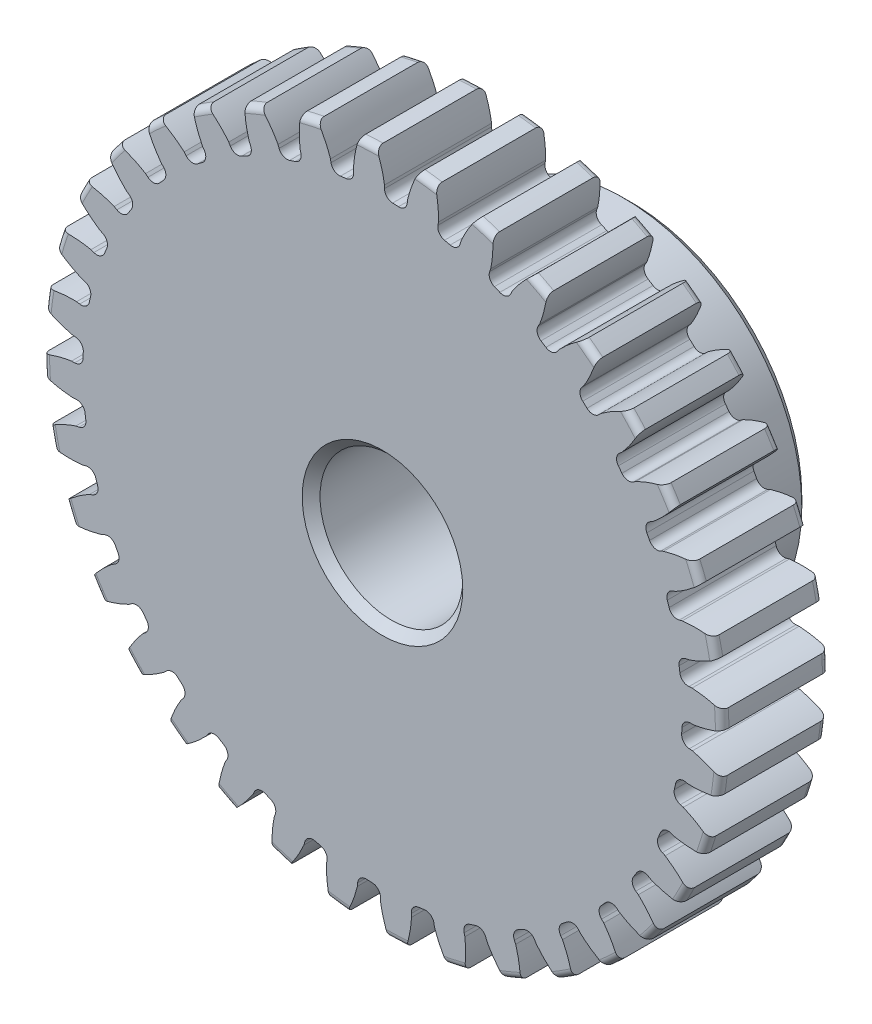
SolidWorks part; units mm, degrees
ref_plane "Front" through (0, 0, 0) normal (0, 0, 1) x (1, 0, 0)
ref_plane "Top" through (0, 0, 0) normal (0, 1, 0) x (1, 0, 0)
ref_plane "Right" through (0, 0, 0) normal (1, 0, 0) x (0, 0, -1)
sketch "Sketch1" plane through (0, 0, 0) normal (0, 0, 1) x (1, 0, 0)
  line L0 (-457.2, 0) -> (457.2, 0) construction
  circle A0 centre (0, 0) radius 15.113
  circle A1 centre (0, 0) radius 14.2875 construction
  circle A3 centre (0, 0) radius 13.3271 construction
  dimension "D1" = 1.7859
  dimension "OD" = 30.226
  dimension "Ptich Dia" = 28.575
  dimension "Root Dia" = 26.6541
  dimension "D3" = 0.8255
  dimension "Number of Teeth" = 914.4
extrude "Boss-Extrude1" add sketch "Sketch1" against normal blind 4.7625
sketch "Sketch2" plane through (0, 0, 0) normal (1, 0, 0) x (0, 0, -1)
  line L0 (4.7625, 0) -> (11.1125, 0)
  line L1 (4.7625, 0) -> (4.7625, 7.9375)
  line L2 (4.7625, 7.9375) -> (11.1125, 7.9375)
  line L3 (11.1125, 7.9375) -> (11.1125, 0)
  point P5 (11.1125, -7.9375)
  point P6 (0, -15.113)
  point P7 (4.7625, -15.113)
  point P9 (0, 15.113)
  dimension "Face Wd" = 4.7625
  dimension "B Hub Dia" = 15.875
  dimension "D O'all Lg." = 11.1125
revolve "Revolve1" add sketch "Sketch2" angle 360 about L0
fillet "Fillet2" radius 0.3023 3 edges at (15.113, 0, -4.7625) (15.113, 0, 0) (7.9375, 0, -4.7625)
sketch "Sketch3" plane through (0, 0, 0) normal (0, 0, 1) x (1, 0, 0)
  line L0 (0, 0) -> (0, 15.113) construction
  line L1 (-3.4634, 13.3918) -> (0, 14.2875)
  line L2 (-9.5921, 14.2875) -> (9.5921, 14.2875) construction
  line L3 (-9.2865, 11.8858) -> (9.2865, 16.6892) construction
  line L4 (-3.4634, 13.3918) -> (0, 0) construction
  line L5 (-8.8339, 10.6442) -> (0, 0) construction
  line L6 (-8.8339, 10.6442) -> (-1.4209, 16.7964) construction
  line L7 (-2.415, 13.62) -> (0, 0) construction
  line L8 (-2.415, 13.62) -> (0.0507, 14.0572) construction
  arc A0 (-3.4634, 13.3918) -> (-8.8339, 10.6442) centre (0, 0) ccw
  circle A1 centre (0, 0) radius 14.2875 construction
  circle A2 centre (0, 0) radius 13.8324 construction
  arc A3 (-3.4634, 13.3918) -> (-2.415, 13.62) centre (0, 0) cw
  circle A4 centre (0, 0) radius 15.113 construction
  point P6 (0, 14.2875)
  dimension "D1" = 3.5773
  dimension "Pressure Angle" = 14.5
  dimension "D2" = 6.0814
  dimension "D3" = 9.6333
  dimension "D4" = 1.0732
  dimension "D5" = 2.5041
sketch "Sketch4" plane through (0, 0, 0) normal (0, 0, 1) x (1, 0, 0)
  line L0 (0, 0) -> (0.6226, 14.2603) construction
  line L1 (0.0898, 13.8321) -> (0.0898, 13.3268)
  line L2 (0, 14.2875) -> (1.2452, 14.2331) construction
  line L3 (1.1161, 13.7873) -> (1.072, 13.2839)
  line L4 (0.0898, 13.3268) -> (0, 0) construction
  line L5 (0, 0) -> (0, 15.113) construction
  line L6 (-8.8339, 10.6442) -> (-1.4209, 16.7964) construction
  line L7 (-8.8339, 10.6442) -> (-1.4209, 16.7964) construction
  arc A0 (1.072, 13.2839) -> (0.0898, 13.3268) centre (0, 0) ccw
  arc A1 (0, 14.2875) -> (1.2452, 14.2331) centre (0, 0) cw construction
  circle A2 centre (0, 0) radius 14.2875 construction
  circle A3 centre (0, 0) radius 13.8324 construction
  circle A4 centre (0, 0) radius 13.3271 construction
  arc A5 (2.8794, 16.6086) -> (-1.4209, 16.7964) centre (0, 0) ccw
  spline S0 degree 2 poles (-1.4209, 16.7964) (-0.1618, 15.4883) (0.0898, 13.8321) knots 0 0 0 1 1 1
  spline S1 degree 2 poles (2.8794, 16.6086) (1.5111, 15.4152) (1.1161, 13.7873) knots 0 0 0 1 1 1
  dimension "D1" = 1.2468
extrude "Cut-Extrude1" cut sketch "Sketch4" against normal through all
fillet "Fillet1" radius 0.374 2 edges at (1.072, 13.2839, -2.3813) (0.0898, 13.3268, -2.3813)
pattern_circular "CirPattern1" count 36 over 360 about axis through (0, 0, -4.7625) along (0, 0, 1) of "Cut-Extrude1", "Fillet1"
sketch "Sketch5" plane through (0, 0, 0) normal (0, 0, 1) x (1, 0, 0)
  circle A0 centre (0, 0) radius 3.175
  circle A1 centre (0, 0) radius 1.5875 construction
  dimension "Bore Min" = 6.35
  dimension "Bore Max" = 3.175
extrude "Cut-Extrude2" cut sketch "Sketch5" against normal through all
chamfer "Chamfer1" distance 0.3969 angle 45 3 edges at (7.9375, 0, -11.1125) (3.175, 0, 0) (3.175, 0, -11.1125)
sketch "Pitch Dia" plane through (0, 0, 0) normal (0, 0, 1) x (1, 0, 0)
  circle A0 centre (0, 0) radius 14.2875 construction
  circle A1 centre (0, 0) radius 14.2875 construction
equation "\"D1@Boss-Extrude1\" = \"Face Wd@Sketch2\""
equation "\"D2@Sketch3\" = \"D1@Sketch3\"*1.7"
equation "\"D3@Sketch3\" = \"D1@Sketch3\"+\"D2@Sketch3\"-.001"
equation "\"D4@Sketch3\" = \"D1@Sketch3\"*.3"
equation "\"D5@Sketch3\" = \"D1@Sketch3\"-\"D4@Sketch3\""
equation "\"D1@Sketch4\" = 1.5708/(\"Number of Teeth@Sketch1\"/\"Ptich Dia@Sketch1\")"
equation "\"D1@Chamfer1\" = \"B Hub Dia@Sketch2\"*.025"
equation "\"D1@CirPattern1\" = \"Number of Teeth@Sketch1\""
equation "\"D1@Fillet1\" = \"D1@Sketch4\"*.3"
equation "\"D1@Fillet2\" = \"OD@Sketch1\"*.01"
equation "\"D1@Sketch1\" = 2.250/(\"Number of Teeth@Sketch1\"/\"Ptich Dia@Sketch1\")"
